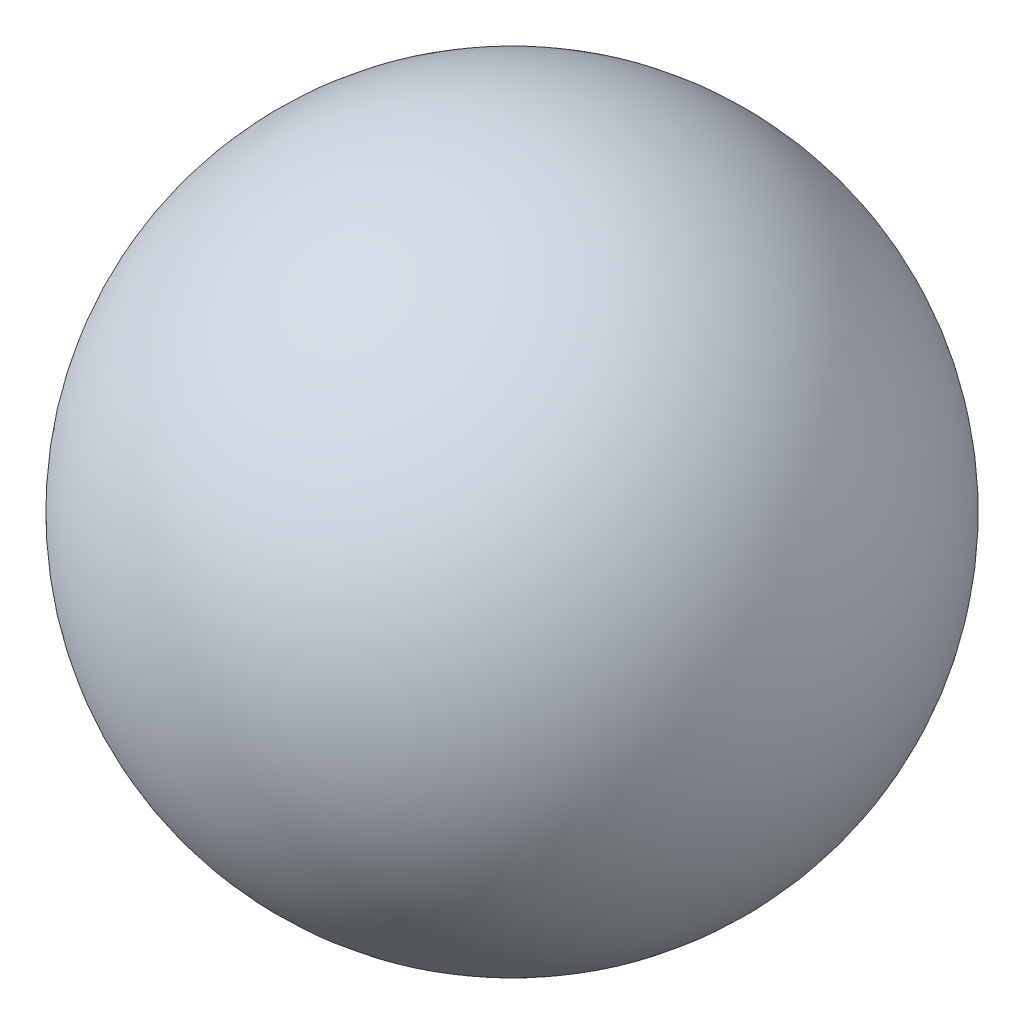
SolidWorks part; units mm, degrees
material "ABS PC"
ref_plane "Front Plane" through (0, 0, 0) normal (0, 0, 1) x (1, 0, 0)
ref_plane "Top Plane" through (0, 0, 0) normal (0, 1, 0) x (1, 0, 0)
ref_plane "Right Plane" through (0, 0, 0) normal (1, 0, 0) x (0, 0, -1)
sketch "Sketch1" plane through (0, 0, 0) normal (0, 0, 1) x (1, 0, 0)
  line L0 (0, 10) -> (0, -10)
  arc A0 (0, -10) -> (0, 10) centre (0, 0) ccw
  dimension "D1" = 10
revolve "Revolve1" add sketch "Sketch1" angle 360 about L0
